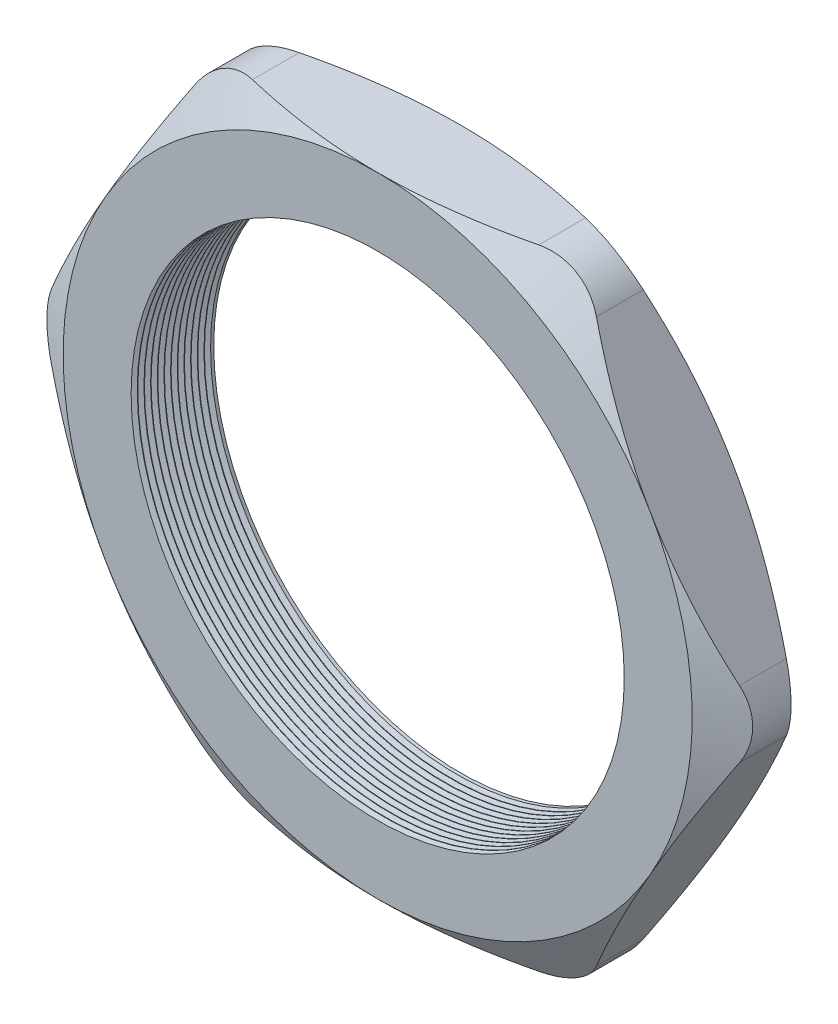
SolidWorks part; units mm, degrees
ref_plane "Front Plane" through (0, 0, 0) normal (0, 0, 1) x (1, 0, 0)
ref_plane "Top Plane" through (0, 0, 0) normal (0, 1, 0) x (1, 0, 0)
ref_plane "Right Plane" through (0, 0, 0) normal (1, 0, 0) x (0, 0, -1)
sketch "Sketch1" plane through (0, 0, 0) normal (0, 0, 1) x (1, 0, 0)
  line L1 (-34.6087, 0) -> (-17.3043, -29.972)
  line L2 (-17.3043, -29.972) -> (17.3043, -29.972)
  line L3 (17.3043, -29.972) -> (34.6087, 0)
  line L4 (34.6087, 0) -> (17.3043, 29.972)
  line L5 (17.3043, 29.972) -> (-17.3043, 29.972)
  line L6 (-17.3043, 29.972) -> (-34.6087, 0)
  circle A0 centre (0, 0) radius 29.972 construction
  circle A1 centre (0, 0) radius 23.495
  dimension "TS" = 46.99
  dimension "H" = 59.944
extrude "Extrude1" add sketch "Sketch1" along normal blind 7.874
sketch "Sketch2" plane through (0, 0, 7.874) normal (0, 0, 1) x (1, 0, 0)
  line L0 (17.3043, 29.972) -> (-17.3043, 29.972) construction
  circle A0 centre (0, 0) radius 29.972
extrude "Cut-Extrude1" cut sketch "Sketch2" against normal through all draft 60 flip side to cut
sketch "Sketch3" plane through (0, 0, 0) normal (0, 0, -1) x (-1, 0, 0)
  line L0 (-17.3043, 29.972) -> (17.3043, 29.972) construction
  circle A0 centre (0, 0) radius 29.972
extrude "Cut-Extrude2" cut sketch "Sketch3" against normal through all draft 60 flip side to cut
fillet "Fillet1" radius 6.35 6 edges at (34.6087, 0, 3.937) (17.3043, -29.972, 3.937) (-17.3043, -29.972, 3.937) (-34.6087, 0, 3.937) (-17.3043, 29.972, 3.937) (17.3043, 29.972, 3.937)
sketch "Sketch4" plane through (0, 0, 0) normal (0, 1, 0) x (1, 0, 0)
  line L0 (-23.495, -7.874) -> (-23.495, -7.2874)
  line L1 (-23.495, 0) -> (-23.495, -7.874) construction
  line L2 (-23.495, -7.2874) -> (-24.003, -7.5807)
  line L3 (-24.003, -7.5807) -> (-23.495, -7.874)
  dimension "D1" = 60
  dimension "D2" = 60
  dimension "D3" = 0.508
revolve "Cut-Revolve1" cut sketch "Sketch4" angle 360 about axis through (0, 0, 0) along (0, 0, 1)
pattern_linear "LPattern1" count 12 spacing 0.635 along (0, 0, -1) of "Cut-Revolve1"
